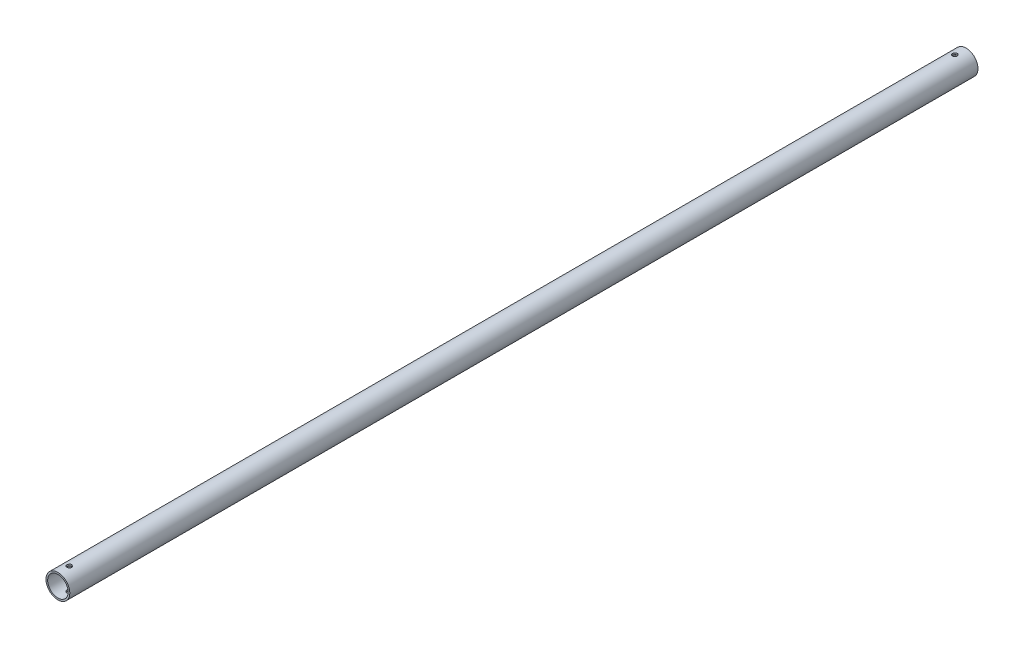
SolidWorks part; units mm, degrees
material "1060 Alloy"
ref_plane "Front Plane" through (0, 0, 0) normal (0, 0, 1) x (1, 0, 0)
ref_plane "Top Plane" through (0, 0, 0) normal (0, 1, 0) x (1, 0, 0)
ref_plane "Right Plane" through (0, 0, 0) normal (1, 0, 0) x (0, 0, -1)
sketch "Sketch1" plane through (0, 0, 0) normal (0, 0, 1) x (1, 0, 0)
  circle A0 centre (0, 0) radius 6.35
  circle A1 centre (0, 0) radius 5.461
  dimension "D1" = 12.7
  dimension "D2" = 10.922
extrude "Boss-Extrude1" add sketch "Sketch1" along normal mid plane 484
sketch "Sketch2" plane through (0, 0, 0) normal (0, 1, 0) x (1, 0, 0)
  line L0 (0, 242) -> (0, 236) construction
  line L1 (5.461, 242) -> (-5.461, 242) construction
  circle A0 centre (0, 236) radius 1.25
  dimension "D1" = 2.5
  dimension "D2" = 6
extrude "Cut-Extrude1" cut sketch "Sketch2" against normal through all both and the other way through all
mirror "Mirror1" about plane through (0, 0, 0) normal (0, 0, 1) of "Cut-Extrude1"
